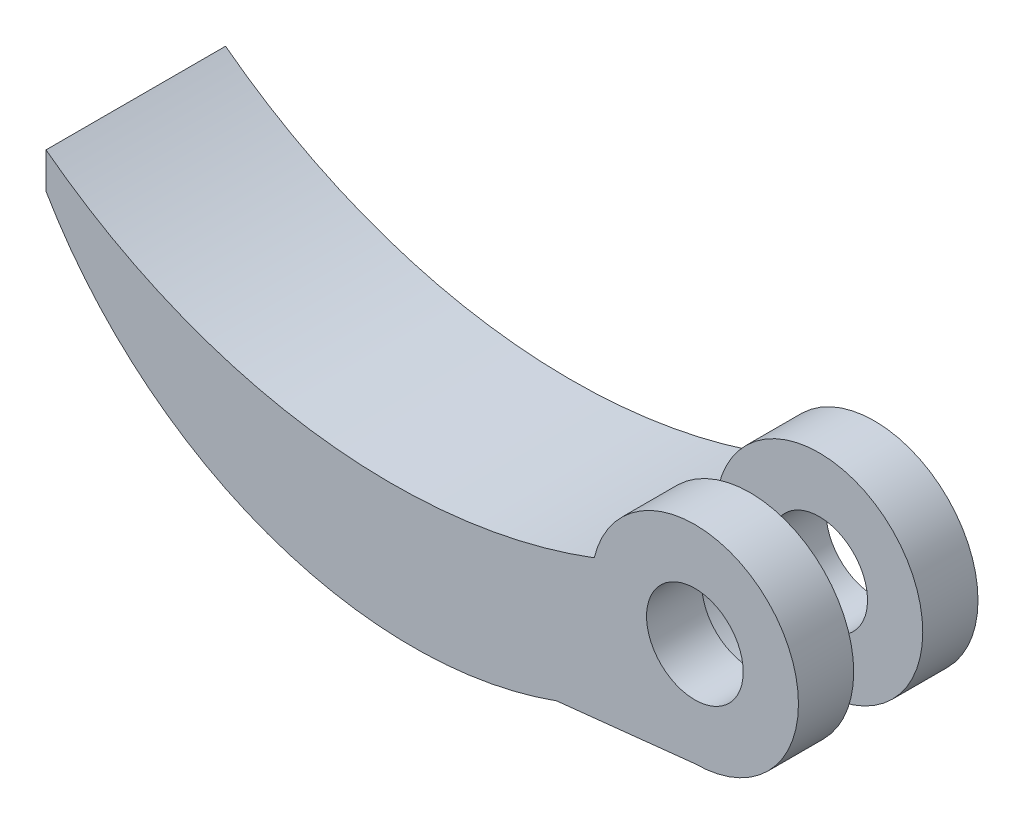
SolidWorks part; units mm, degrees
material "AISI 304"
ref_plane "Alzado" through (0, 0, 0) normal (0, 0, 1) x (1, 0, 0)
ref_plane "Planta" through (0, 0, 0) normal (0, 1, 0) x (1, 0, 0)
ref_plane "Vista lateral" through (0, 0, 0) normal (1, 0, 0) x (0, 0, -1)
sketch "Croquis1" plane through (0, 0, 0) normal (0, 0, 1) x (1, 0, 0)
  circle A0 centre (0, 0) radius 3.5
  circle A1 centre (0, 0) radius 7.5
  dimension "D1" = 7
  dimension "D2" = 15
extrude "Saliente-Extruir1" add sketch "Croquis1" along normal blind 4
sketch "Croquis2" plane through (0, 0, 0) normal (0, 0, -1) x (-1, 0, 0)
  circle A0 centre (0, 0) radius 2.1938
extrude "Saliente-Extruir2" add sketch "Croquis2" along normal blind 5 separate body
sketch "Croquis3" plane through (0, 0, -5) normal (0, 0, -1) x (-1, 0, 0)
  circle A0 centre (0, 0) radius 3.5
  circle A1 centre (0, 0) radius 7.5
  dimension "D1" = 7
  dimension "D2" = 15
extrude "Saliente-Extruir3" add sketch "Croquis3" along normal blind 4 separate body
sketch "Croquis4" plane through (0, 0, -5) normal (0, 0, -1) x (-1, 0, 0)
  circle A0 centre (0, 0) radius 2.1938
extrude "Cortar-Extruir1" cut sketch "Croquis4" against normal blind 14
sketch "Croquis5" plane through (0, 0, 4) normal (0, 0, 1) x (1, 0, 0)
  line L2 (-10.0093, -8.5669) -> (0, -7.5)
  line L3 (-46.9818, 4.9039) -> (-46.9818, 7.5)
  circle A0 centre (0, 0) radius 7.5 construction
  arc A1 (-10.0093, -8.5669) -> (-46.9818, 4.9039) centre (-20.4372, 20.2857) cw
  arc A2 (-7.2888, 1.7674) -> (-46.9818, 7.5) centre (-21.9545, 40.5062) cw
  arc A3 (-7.2888, 1.7674) -> (0, -7.5) centre (0, 0) ccw
  point P9 (0, 0)
  point P10 (-7.2888, 1.7674)
extrude "Saliente-Extruir4" add sketch "Croquis5" against normal blind 13
